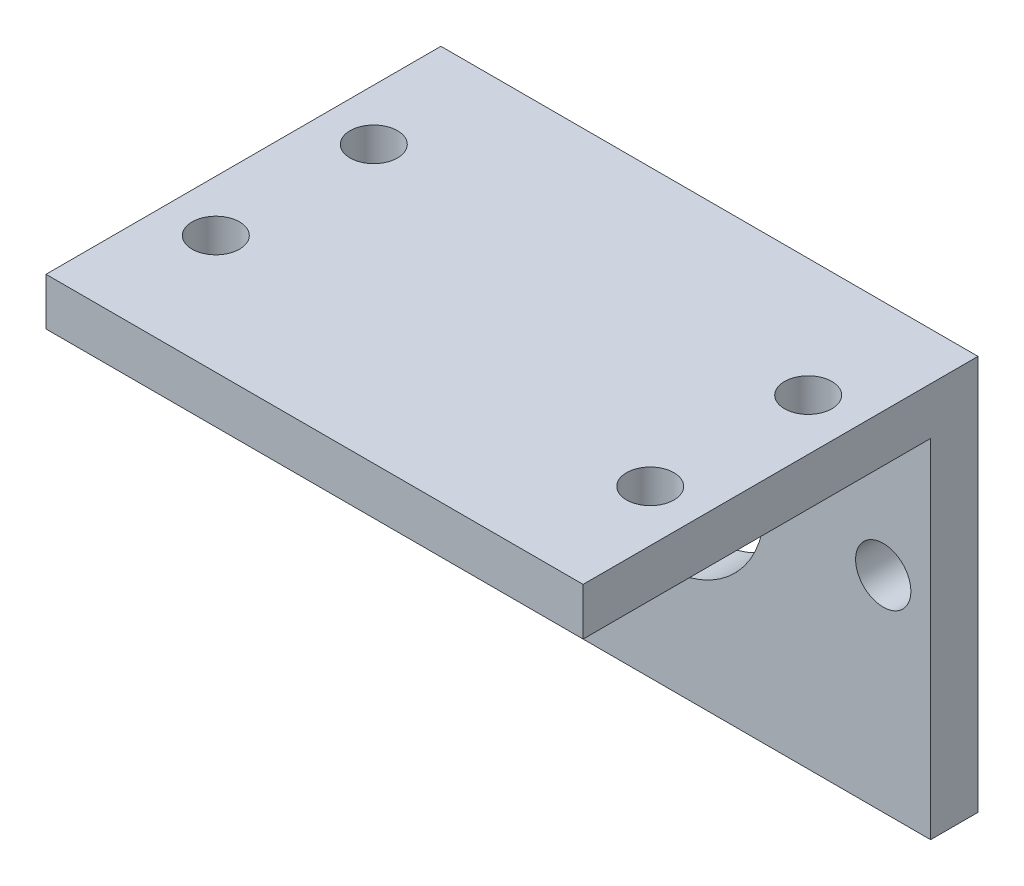
SolidWorks part; units mm, degrees
material "6061 合金"
ref_plane "前视基准面" through (0, 0, 0) normal (0, 0, 1) x (1, 0, 0)
ref_plane "上视基准面" through (0, 0, 0) normal (0, 1, 0) x (1, 0, 0)
ref_plane "右视基准面" through (0, 0, 0) normal (1, 0, 0) x (0, 0, -1)
sketch "草图1" plane through (0, 0, 0) normal (0, 1, 0) x (1, 0, 0)
  line L0 (0, 0) -> (0, 76.0239) construction
  line L1 (0, 0) -> (50.0233, 0) construction
  line L2 (-34, 50) -> (34, 50)
  line L3 (-34, 50) -> (-34, 0)
  line L4 (-34, 0) -> (34, 0)
  line L5 (34, 50) -> (34, 0)
  line L7 (-27.5, 35) -> (27.5, 35) construction
  line L8 (-27.5, 35) -> (-27.5, 15) construction
  line L9 (-27.5, 15) -> (27.5, 15) construction
  line L10 (27.5, 35) -> (27.5, 15) construction
  circle A0 centre (-27.5, 35) radius 3
  circle A1 centre (27.5, 35) radius 3
  circle A2 centre (-27.5, 15) radius 3
  circle A3 centre (27.5, 15) radius 3
  dimension "D6" = 6
  dimension "D7" = 6
  dimension "D8" = 6
  dimension "D9" = 6
  dimension "D1" = 68
  dimension "D2" = 50
  dimension "D3" = 55
  dimension "D4" = 20
  dimension "D5" = 15
extrude "凸台-拉伸1" add sketch "草图1" along normal blind 6
sketch "草图3" plane through (0, 6, 0) normal (0, 1, 0) x (1, 0, 0)
  line L0 (-34, 50) -> (-34, 0) construction
  line L1 (-34, 50) -> (34, 50)
  line L2 (-34, 50) -> (-34, 44)
  line L3 (-34, 44) -> (34, 44)
  line L4 (34, 50) -> (34, 44)
  line L5 (34, 50) -> (-34, 50) construction
  dimension "D1" = 68
  dimension "D2" = 6
extrude "凸台-拉伸2" add sketch "草图3" against normal blind 50
sketch "草图4" plane through (0, 0, -44) normal (0, 0, 1) x (1, 0, 0)
  line L0 (0, 0) -> (0, -44) construction
  line L1 (-34, -44) -> (34, -44) construction
  line L2 (0, -18) -> (28, -18) construction
  line L4 (34, 6) -> (-34, 6) construction
  circle A0 centre (0, -18) radius 13
  circle A1 centre (28, -18) radius 3.5
  circle A2 centre (-28, -18) radius 3.5
  dimension "D1" = 26
  dimension "D2" = 24
  dimension "D3" = 7
  dimension "D4" = 28
extrude "切除-拉伸1" cut sketch "草图4" against normal up to next
